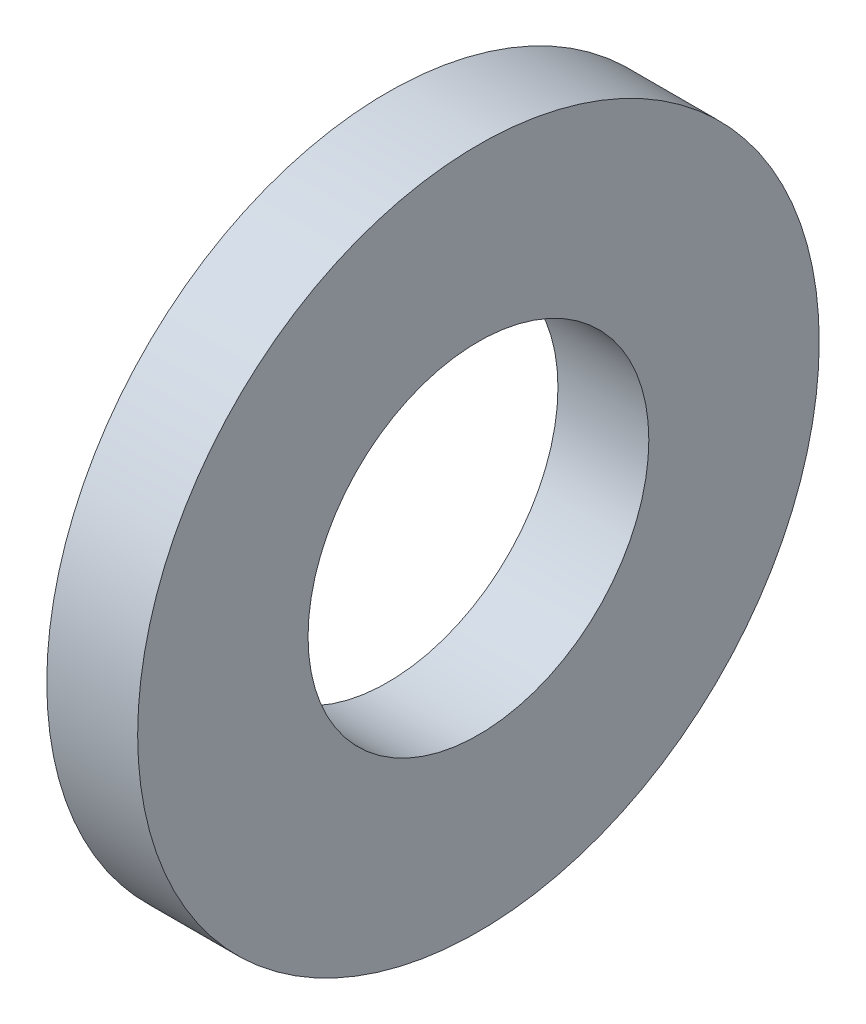
SolidWorks part; units mm, degrees
ref_plane "Face" through (0, 0, 0) normal (0, 0, 1) x (1, 0, 0)
ref_plane "Dessus" through (0, 0, 0) normal (0, 1, 0) x (1, 0, 0)
ref_plane "Droite" through (0, 0, 0) normal (1, 0, 0) x (0, 0, -1)
sketch "Esquisse1" plane through (0, 0, 0) normal (0, 0, 1) x (1, 0, 0)
  line L0 (-16.7064, 7.5) -> (-14.7064, 7.5)
  line L1 (-14.7064, 7.5) -> (-14.7064, 3.75)
  line L2 (-14.7064, 3.75) -> (-16.7064, 3.75)
  line L3 (-16.7064, 3.75) -> (-16.7064, 7.5)
  line L4 (-42.6301, 0) -> (31.6845, 0) construction
revolve "Révolution1" add sketch "Esquisse1" angle 360 about L4
